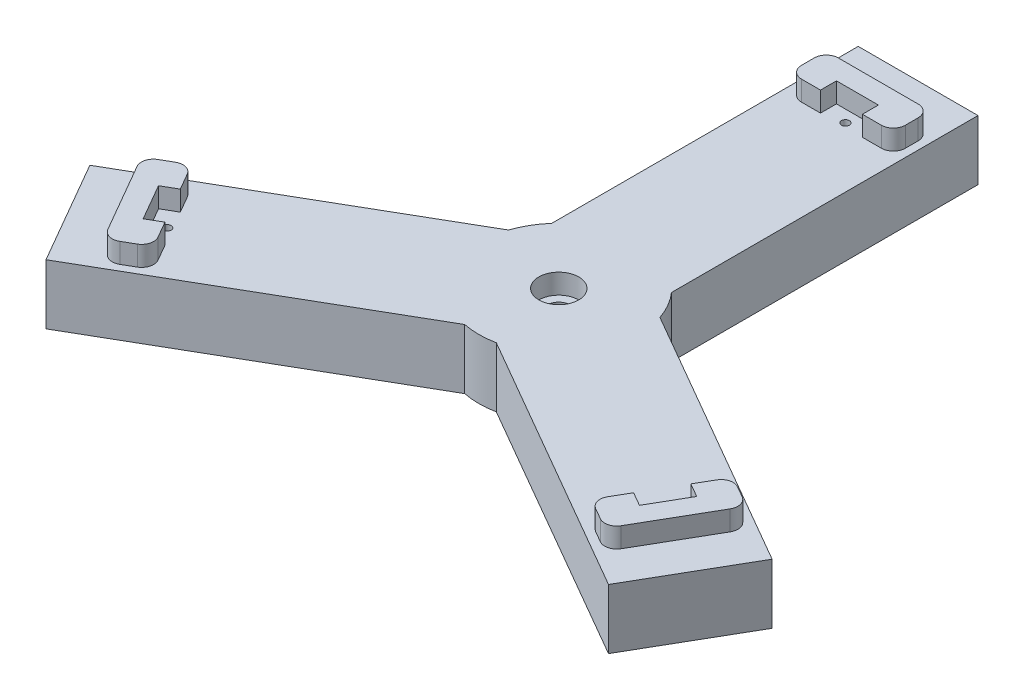
SolidWorks part; units mm, degrees
ref_plane "Front Plane" through (0, 0, 0) normal (0, 0, 1) x (1, 0, 0)
ref_plane "Top Plane" through (0, 0, 0) normal (0, 1, 0) x (1, 0, 0)
ref_plane "Right Plane" through (0, 0, 0) normal (1, 0, 0) x (0, 0, -1)
sketch "Sketch5" plane through (0, 0, 0) normal (0, 1, 0) x (1, 0, 0)
  circle A0 centre (0, 0) radius 20
  dimension "D1" = 40
extrude "Boss-Extrude2" add sketch "Sketch5" along normal blind 15
sketch "Sketch6" plane through (0, 0, 0) normal (0, 1, 0) x (1, 0, 0)
  line L0 (0, -11) -> (0, 11) construction
  line L1 (15, 0) -> (-15, 0)
  line L2 (15, 0) -> (15, 90)
  line L3 (15, 90) -> (-15, 90)
  line L4 (-15, 0) -> (-15, 90)
  dimension "D1" = 90
  dimension "D2" = 15
  dimension "D3" = 15
extrude "Boss-Extrude3" add sketch "Sketch6" along normal blind 15
pattern_circular "CirPattern1" count 3 over 360 about axis through (0, 0, 0) along (0, 1, 0) of "Boss-Extrude3"
sketch "Sketch7" plane through (0, 15, 0) normal (0, 1, 0) x (1, 0, 0)
  line L0 (0, -11) -> (0, 11) construction
  line L1 (-13, 80) -> (13, 80)
  line L2 (-13, 80) -> (-13, 70.8)
  line L3 (-13, 70.8) -> (-5.25, 70.8)
  line L4 (13, 80) -> (13, 70.8)
  line L5 (5.25, 70.8) -> (5.25, 74.8)
  line L6 (5.25, 74.8) -> (-5.25, 74.8)
  line L7 (-5.25, 74.8) -> (-5.25, 70.8)
  line L8 (-11, 0) -> (11, 0) construction
  line L9 (5.25, 70.8) -> (13, 70.8)
  point P8 (5.25, 72.8)
  dimension "D1" = 26
  dimension "D2" = 13
  dimension "D3" = 9.2
  dimension "D4" = 5.25
  dimension "D5" = 4
  dimension "D6" = 5.25
  dimension "D7" = 80
extrude "Boss-Extrude4" add sketch "Sketch7" along normal blind 5
fillet "Fillet1" radius 3 4 edges at (13, 17.5, -70.8) (13, 17.5, -80) (-13, 17.5, -70.8) (-13, 17.5, -80)
sketch "Sketch8" plane through (0, 15, 0) normal (0, 1, 0) x (1, 0, 0)
  line L0 (5.25, 70.8) -> (10, 70.8) construction
  circle A0 centre (0, 71.8) radius 1
  dimension "D1" = 2
  dimension "D2" = 1
extrude "Cut-Extrude1" cut sketch "Sketch8" against normal through all
sketch "Sketch9" plane through (0, 0, 0) normal (0, -1, 0) x (1, 0, 0)
  circle A0 centre (0, -71.8) radius 10
  dimension "D1" = 20
extrude "Cut-Extrude2" cut sketch "Sketch9" against normal blind 10 contours A0
pattern_circular "CirPattern4" count 3 over 360 about axis through (0, 0, 0) along (0, 1, 0) of "Boss-Extrude4", "Fillet1"
pattern_circular "CirPattern6" count 3 over 360 about axis through (0, 0, 0) along (0, 1, 0) of "Cut-Extrude1", "Cut-Extrude2"
sketch "Sketch11" plane through (0, 0, 0) normal (0, 1, 0) x (1, 0, 0)
  circle A0 centre (0, 0) radius 2.875
  dimension "D1" = 5.75
extrude "Cut-Extrude4" cut sketch "Sketch11" along normal up to next
sketch "Sketch13" plane through (0, 0, 0) normal (0, -1, 0) x (1, 0, 0)
  line L1 (-9, -9) -> (9, -9)
  line L2 (-9, -9) -> (-9, 9)
  line L3 (-9, 9) -> (9, 9)
  line L4 (9, -9) -> (9, 9)
  line L5 (-9, -9) -> (9, 9) construction
  line L6 (-9, 9) -> (9, -9) construction
  point P0 (0, 0)
  dimension "D1" = 18
  dimension "D2" = 18
extrude "Cut-Extrude5" cut sketch "Sketch13" against normal blind 5
fillet "Fillet2" radius 5 4 edges at (-9, 2.5, -9) (9, 2.5, -9) (9, 2.5, 9) (-9, 2.5, 9)
sketch "Sketch14" plane through (0, 15, 0) normal (0, 1, 0) x (1, 0, 0)
  circle A0 centre (0, 0) radius 5
  dimension "D1" = 10
extrude "Cut-Extrude6" cut sketch "Sketch14" against normal blind 5
